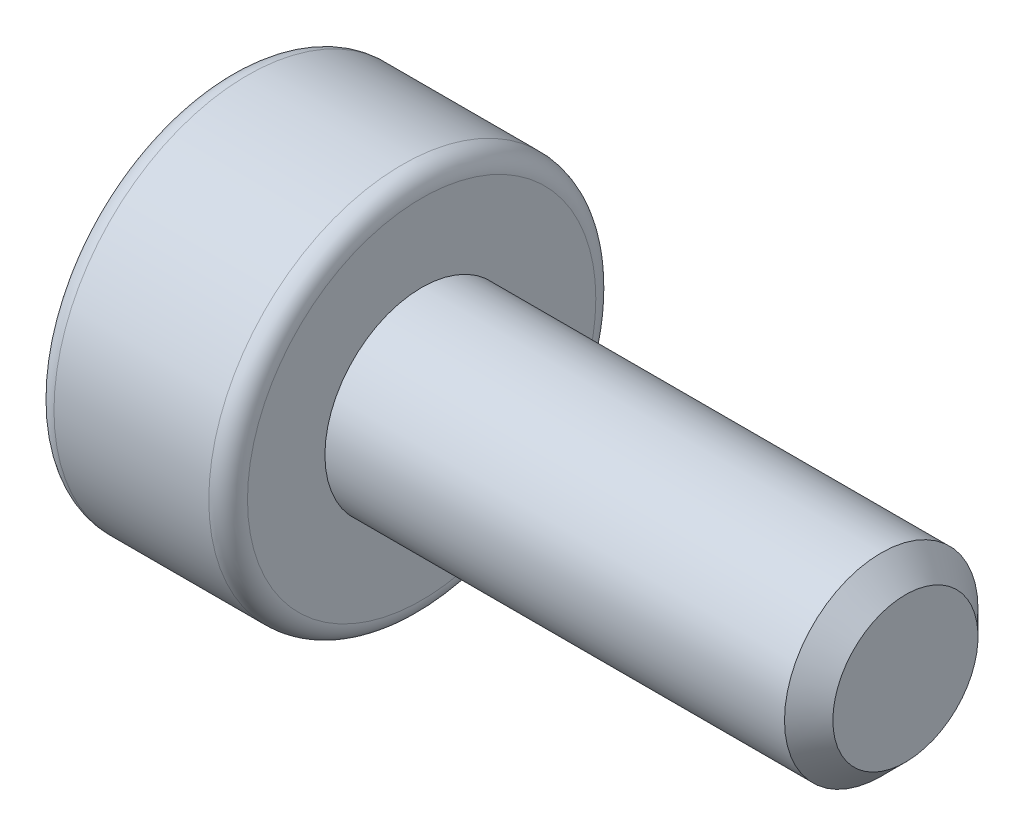
SolidWorks part; units mm, degrees
ref_plane "Front Plane" through (0, 0, 0) normal (0, 0, 1) x (1, 0, 0)
ref_plane "Top Plane" through (0, 0, 0) normal (0, 1, 0) x (1, 0, 0)
ref_plane "Right Plane" through (0, 0, 0) normal (1, 0, 0) x (0, 0, -1)
sketch "Sketch2" plane through (0, 0, 0) normal (0, 0, 1) x (1, 0, 0)
  line L0 (0, 0) -> (0, 1.8)
  line L1 (2, 1) -> (2, 1.8)
  line L2 (1.8, 2) -> (0.2, 2)
  line L3 (2, 1) -> (6.75, 1)
  line L4 (6.75, 1) -> (7, 0.75)
  line L5 (7, 0.75) -> (7, 0)
  line L6 (7, 0) -> (0, 0)
  line L7 (-2.2818, 0) -> (8.0811, 0) construction
  arc A0 (2, 1.8) -> (1.8, 2) centre (1.8, 1.8) ccw
  arc A1 (0, 1.8) -> (0.2, 2) centre (0.2, 1.8) cw
  point P13 (2, 2)
  point P16 (0, 2)
  dimension "D7" = 0.2
  dimension "D1" = 4
  dimension "D2" = 2
  dimension "D3" = 5
  dimension "D4" = 135
  dimension "D5" = 0.25
  dimension "D6" = 2
revolve "Revolve1" add sketch "Sketch2" angle 360 about L7
sketch "Sketch3" plane through (0, 0, 0) normal (-1, 0, 0) x (0, 0, 1)
  line L1 (0.433, -0.75) -> (0.866, 0)
  line L2 (0.866, 0) -> (0.433, 0.75)
  line L3 (0.433, 0.75) -> (-0.433, 0.75)
  line L4 (-0.433, 0.75) -> (-0.866, 0)
  line L5 (-0.866, 0) -> (-0.433, -0.75)
  line L6 (-0.433, -0.75) -> (0.433, -0.75)
  circle A0 centre (0, 0) radius 0.75 construction
  dimension "D1" = 1.5
extrude "Cut-Extrude1" cut sketch "Sketch3" against normal blind 0.8
